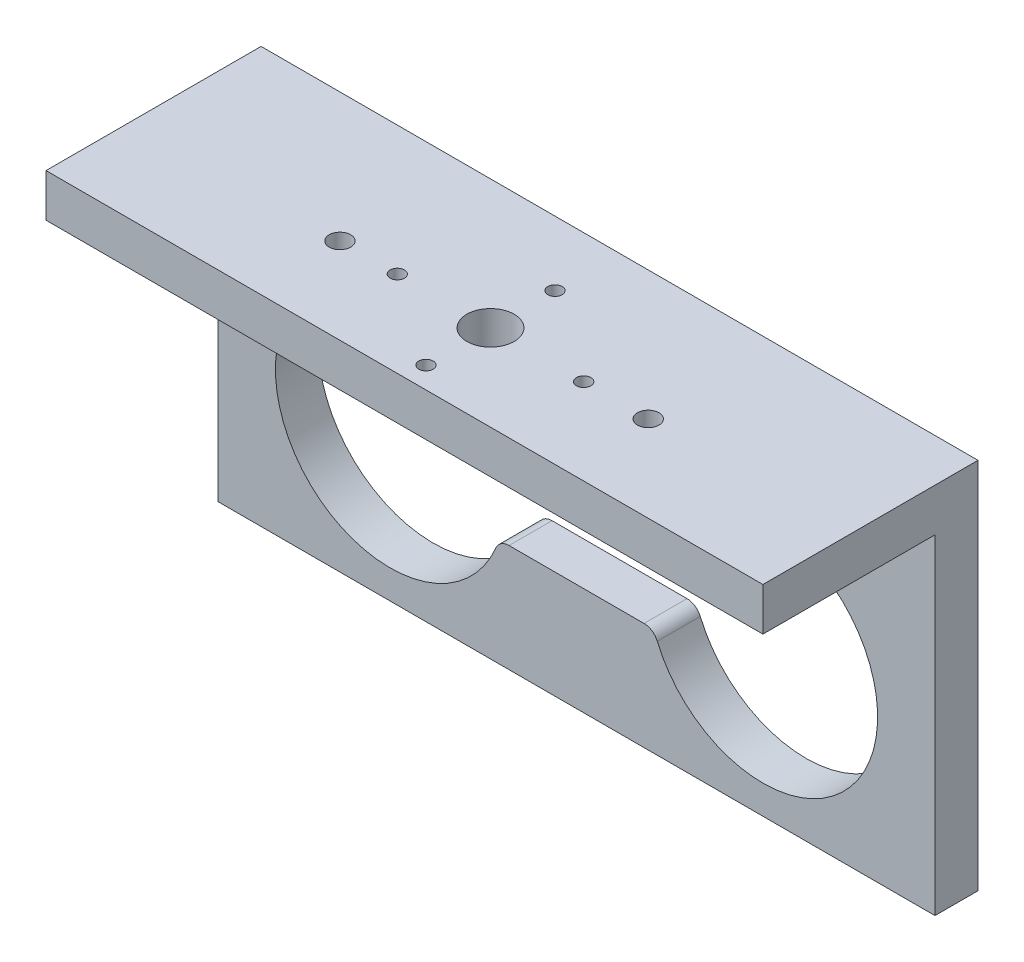
SolidWorks part; units mm, degrees
other "标注1"
sketch "草图6" plane through (25, -10, 15) normal (0.0929, -0.9273, 0.3626) x (0.5024, 0.3581, 0.787)
other "标注2"
sketch "草图7" plane through (25, -10, 15) normal (0.0929, -0.9273, 0.3626) x (0.5024, 0.3581, 0.787)
other "标注3"
sketch "草图8" plane through (25, -10, 15) normal (0.0929, -0.9273, 0.3626) x (0.5024, 0.3581, 0.787)
ref_plane "前视基准面" through (0, 0, 0) normal (0, 0, 1) x (1, 0, 0)
ref_plane "上视基准面" through (0, 0, 0) normal (0, 1, 0) x (1, 0, 0)
ref_plane "右视基准面" through (0, 0, 0) normal (1, 0, 0) x (0, 0, -1)
sketch "草图1" plane through (0, 0, 0) normal (0, 0, 1) x (1, 0, 0)
  line L1 (25, -10) -> (-25, -10)
  line L2 (25, -10) -> (25, 10)
  line L3 (25, 10) -> (-25, 10)
  line L4 (-25, -10) -> (-25, 10)
  line L5 (25, -10) -> (-25, 10) construction
  line L6 (25, 10) -> (-25, -10) construction
  line L8 (-4.7084, 2.5) -> (4.7084, 2.5)
  line L9 (4.7084, -2.5) -> (-4.7084, -2.5)
  line L10 (3.25, 7.25) -> (-3.25, 7.25) construction
  line L11 (3.25, 5.5) -> (-3.25, 5.5)
  line L12 (3.25, 9) -> (-3.25, 9)
  arc A7 (5.6297, -3.1111) -> (5.6297, 3.1111) centre (13, 0) ccw
  arc A8 (-5.6297, 3.1111) -> (-5.6297, -3.1111) centre (-13, 0) ccw
  arc A9 (4.7084, -2.5) -> (5.6297, -3.1111) centre (4.7084, -3.5) cw
  arc A10 (4.7084, 2.5) -> (5.6297, 3.1111) centre (4.7084, 3.5) ccw
  arc A11 (-4.7084, -2.5) -> (-5.6297, -3.1111) centre (-4.7084, -3.5) ccw
  arc A12 (-4.7084, 2.5) -> (-5.6297, 3.1111) centre (-4.7084, 3.5) cw
  arc A13 (3.25, 5.5) -> (3.25, 9) centre (3.25, 7.25) ccw
  arc A14 (-3.25, 9) -> (-3.25, 5.5) centre (-3.25, 7.25) ccw
  point P0 (0, 0)
  point P22 (0, 7.25)
  dimension "D3" = 1
  dimension "D4" = 8
  dimension "D5" = 8
  dimension "D6" = 2.5
  dimension "D8" = 13
  dimension "D9" = 13
  dimension "D12" = 1.75
  dimension "D1" = 20
  dimension "D2" = 50
  dimension "D7" = 2.5
  dimension "D10" = 7.25
  dimension "D11" = 6.5
  dimension "D13" = 3.25
extrude "凸台-拉伸1" add sketch "草图1" along normal blind 3
sketch "草图2" plane through (0, 10, 0) normal (0, 1, 0) x (1, 0, 0)
  line L1 (-25, 0) -> (25, 0)
  line L2 (-25, 0) -> (-25, -15)
  line L3 (-25, -15) -> (25, -15)
  line L4 (25, 0) -> (25, -15)
  dimension "D1" = 15
extrude "凸台-拉伸2" add sketch "草图2" along normal blind 6
sketch "草图5" plane through (0, 10, 0) normal (0, -1, 0) x (1, 0, 0)
  line L1 (25, 3) -> (-25, 3)
  line L2 (25, 3) -> (25, 15)
  line L3 (25, 15) -> (-25, 15)
  line L4 (-25, 3) -> (-25, 15)
extrude "切除-拉伸2" cut sketch "草图5" against normal blind 3
sketch "草图4" plane through (0, 16, 0) normal (0, 1, 0) x (1, 0, 0)
  line L0 (-25, -15) -> (25, -15) construction
  circle A0 centre (0, -9) radius 1.65
  circle A1 centre (6.5, -9) radius 0.5
  circle A2 centre (-6.5, -9) radius 0.5
  circle A3 centre (11, -9) radius 0.75
  circle A4 centre (-10.5, -9) radius 0.75
  circle A5 centre (0, -4.5) radius 0.5
  circle A6 centre (0, -13.5) radius 0.5
  dimension "D1" = 3.3
  dimension "D2" = 1
  dimension "D3" = 6.5
  dimension "D4" = 1
  dimension "D5" = 6.5
  dimension "D6" = 6
  dimension "D7" = 1.5
  dimension "D8" = 1.5
  dimension "D9" = 10.5
  dimension "D10" = 11
  dimension "D11" = 1
  dimension "D12" = 1
  dimension "D13" = 4.5
  dimension "D14" = 4.5
extrude "切除-拉伸1" cut sketch "草图4" against normal up to surface (3 mm away) up to face at (0, 13, 9)
sketch "草图10" plane through (0, 16, 0) normal (0, 1, 0) x (1, 0, 0)
  line L0 (-25, 0) -> (-25, -15) construction
  line L1 (25, 0) -> (-25, 0)
  line L2 (25, 0) -> (25, -3)
  line L3 (25, -3) -> (-25, -3)
  line L4 (-25, 0) -> (-25, -3)
